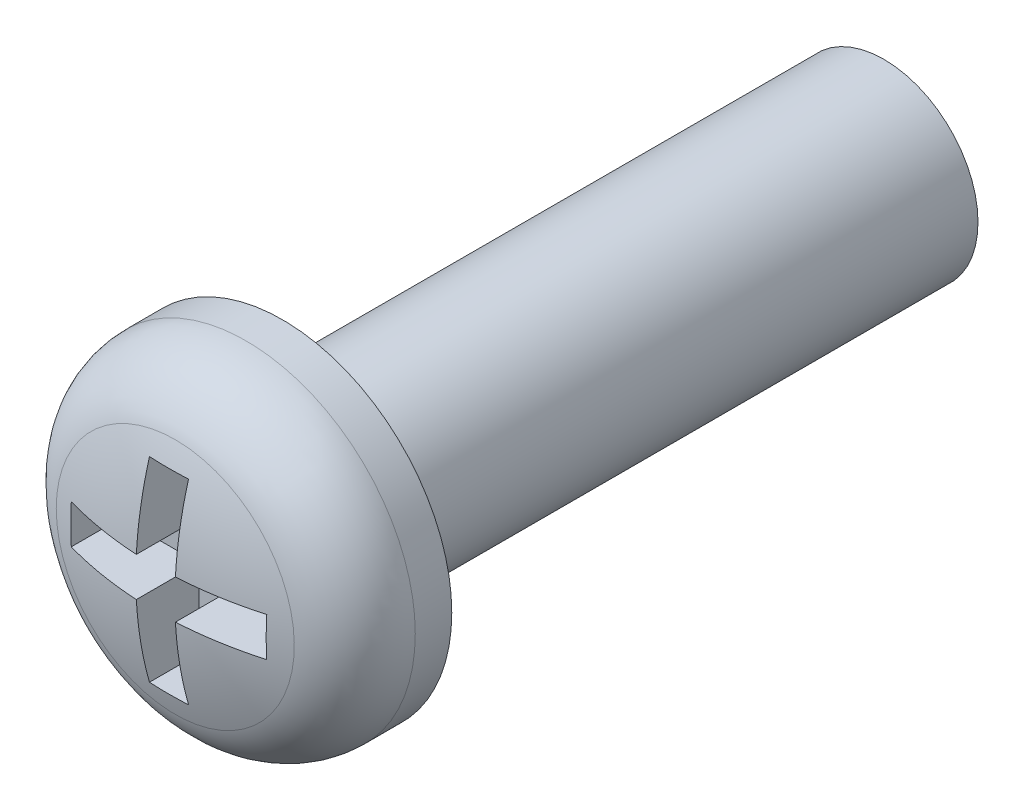
SolidWorks part; units mm, degrees
ref_plane "Front" through (0, 0, 0) normal (0, 0, 1) x (1, 0, 0)
ref_plane "Top" through (0, 0, 0) normal (0, 1, 0) x (1, 0, 0)
ref_plane "Right" through (0, 0, 0) normal (1, 0, 0) x (0, 0, -1)
sketch "Sketch1" plane through (0, 0, 0) normal (1, 0, 0) x (0, 0, -1)
  line L0 (-33.736, 0) -> (50.0028, 0) construction
  line L1 (-1.1333, 2.25) -> (0, 2.25)
  line L2 (0, 2.25) -> (0, 1.25)
  line L3 (0, 1.25) -> (4, 1.25)
  line L6 (4, 0) -> (-1.7, 0)
  line L8 (4, 1.25) -> (4, 0)
  arc A0 (-1.7, 0) -> (-1.1333, 2.25) centre (3.0502, 0) cw
  dimension "k+f" = 1.7
  dimension "dk" = 4.5
  dimension "l" = 4
  dimension "D2" = 1.1333
  dimension "D1" = 2.5
revolve "Revolve1" add sketch "Sketch1" angle 360 about L0
ref_plane "Plane1" through (0, 0, 1.7) normal (0, 0, -1) x (-1, 0, 0)
sketch "Sketch2" plane through (0, 0, 1.7) normal (0, 0, -1) x (-1, 0, 0)
  line L0 (0, 2.0016) -> (0, -1.8677) construction
  line L1 (2.0756, 0) -> (-1.9911, 0) construction
  line L2 (0, 1.3) -> (0.26, 1.3)
  line L3 (0.26, 1.3) -> (0.26, 0.26)
  line L4 (0.26, 0.26) -> (1.3, 0.26)
  line L5 (1.3, 0.26) -> (1.3, 0)
  line L6 (0.26, -1.3) -> (0, -1.3)
  line L7 (0.26, -0.26) -> (0.26, -1.3)
  line L8 (1.3, -0.26) -> (0.26, -0.26)
  line L9 (1.3, 0) -> (1.3, -0.26)
  line L10 (-1.3, -0.26) -> (-1.3, 0)
  line L11 (-0.26, -0.26) -> (-1.3, -0.26)
  line L12 (-0.26, -1.3) -> (-0.26, -0.26)
  line L13 (0, -1.3) -> (-0.26, -1.3)
  line L14 (-0.26, 1.3) -> (0, 1.3)
  line L15 (-0.26, 0.26) -> (-0.26, 1.3)
  line L16 (-1.3, 0.26) -> (-0.26, 0.26)
  line L17 (-1.3, 0) -> (-1.3, 0.26)
  dimension "D1" = 0.26
  dimension "m1/2" = 1.3
  dimension "D3" = 0.26
  dimension "m2/2" = 1.3
extrude "Cut-Extrude2" cut sketch "Sketch2" along normal blind 0.85
fillet "Fillet1" radius 1 1 edges at (2.25, 0, 1.1333)
chamfer "Chamfer1" distance 0.225 1 edges at (1.25, 0, -4)
sketch "Esquisse1" plane through (0, 0, 0) normal (0, 0, -1) x (-1, 0, 0)
  circle A0 centre (0, 0) radius 1.25 construction
  circle A1 centre (0, 0) radius 1.25
  point P0 (0, 0)
extrude "Boss.-Extru.1" add sketch "Esquisse1" along normal blind 8
equation "\"D1@Sketch2\" = \"m1/2@Sketch2\"/5"
equation "\"D3@Sketch2\" = \"m2/2@Sketch2\"/5"
equation "\"D1@Plane1\" = \"k+f@Sketch1\""
equation "\"D1@Cut-Extrude2\" = \"k+f@Sketch1\"/2"
equation "\"D2@Sketch1\" = \"k+f@Sketch1\"*2/3"
